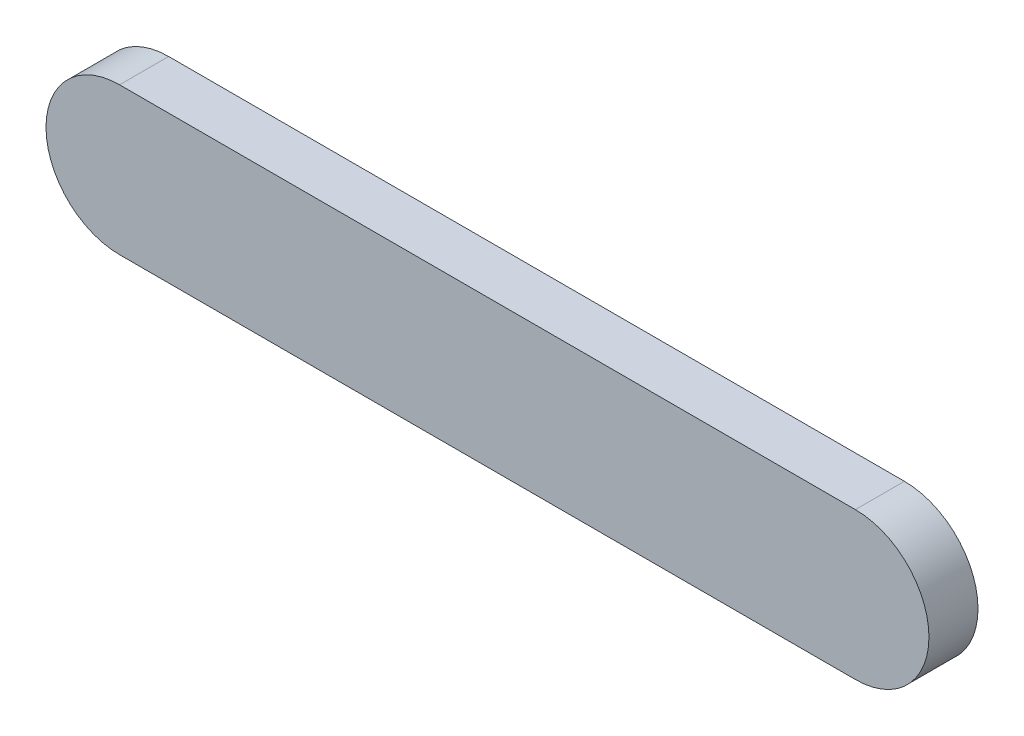
SolidWorks part; units mm, degrees
ref_plane "Front" through (0, 0, 0) normal (0, 0, 1) x (1, 0, 0)
ref_plane "Top" through (0, 0, 0) normal (0, 1, 0) x (1, 0, 0)
ref_plane "Right" through (0, 0, 0) normal (1, 0, 0) x (0, 0, -1)
sketch "Sketch1" plane through (0, 0, 0) normal (0, 0, 1) x (1, 0, 0)
  line L0 (0, 15) -> (150, 15)
  line L2 (150, -15) -> (0, -15)
  arc A1 (0, 15) -> (0, -15) centre (0, 0) ccw
  arc A2 (150, -15) -> (150, 15) centre (150, 0) ccw
  dimension "D1" = 15
  dimension "D2" = 150
extrude "Boss-Extrude1" add sketch "Sketch1" along normal blind 10
